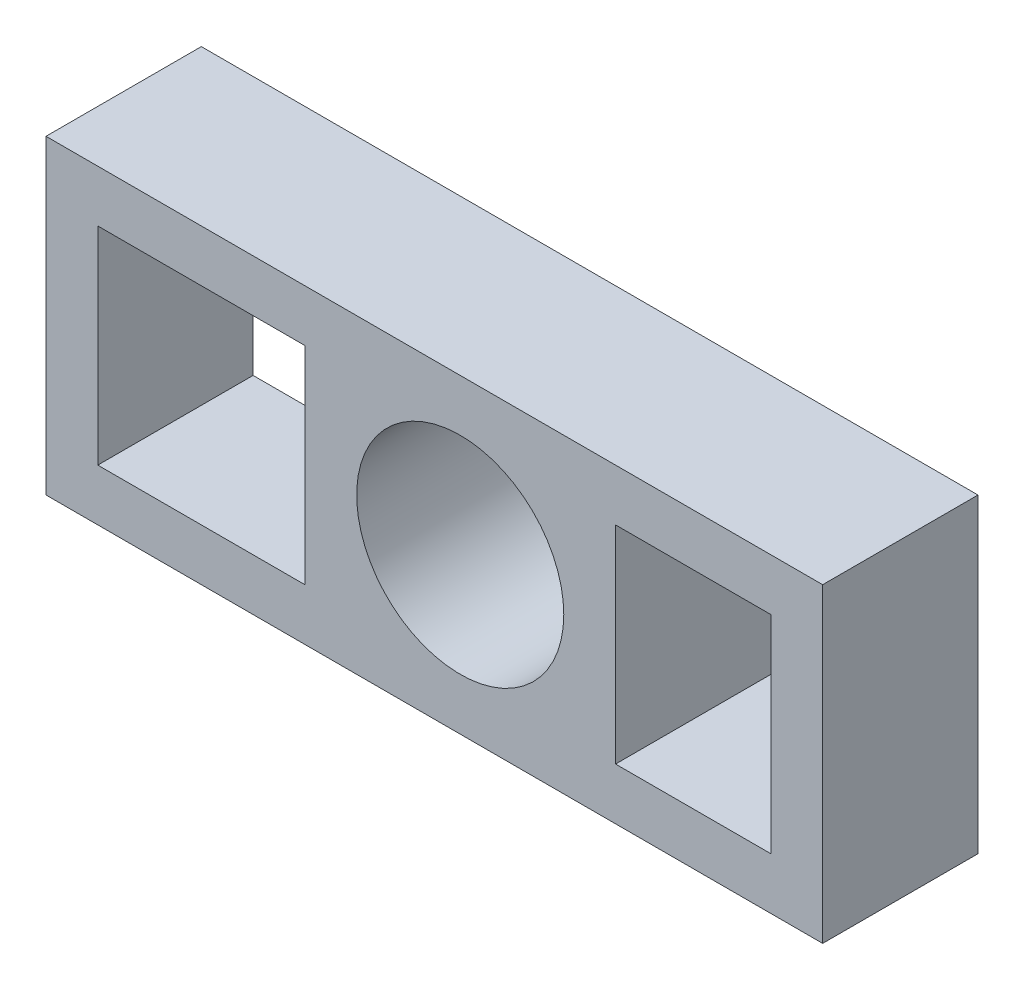
SolidWorks part; units mm, degrees
ref_plane "Front Plane" through (0, 0, 0) normal (0, 0, 1) x (1, 0, 0)
ref_plane "Top Plane" through (0, 0, 0) normal (0, 1, 0) x (1, 0, 0)
ref_plane "Right Plane" through (0, 0, 0) normal (1, 0, 0) x (0, 0, -1)
sketch "Sketch1" plane through (0, 0, 0) normal (0, 0, 1) x (1, 0, 0)
  line L1 (0, 0) -> (1905, 0)
  line L2 (0, 0) -> (0, 762)
  line L3 (0, 762) -> (1905, 762)
  line L4 (1905, 0) -> (1905, 762)
  line L7 (127, 635) -> (635, 635)
  line L8 (127, 635) -> (127, 127)
  line L9 (127, 127) -> (635, 127)
  line L10 (635, 635) -> (635, 127)
  line L20 (1397, 635) -> (1778, 635)
  line L21 (1397, 635) -> (1397, 127)
  line L22 (1397, 127) -> (1778, 127)
  line L23 (1778, 635) -> (1778, 127)
  circle A1 centre (1016, 381) radius 254
  dimension "D9" = 381
  dimension "D3" = 508
  dimension "D1" = 762
  dimension "D2" = 1905
  dimension "D6" = 508
  dimension "D10" = 508
extrude "Boss-Extrude1" add sketch "Sketch1" along normal blind 381
